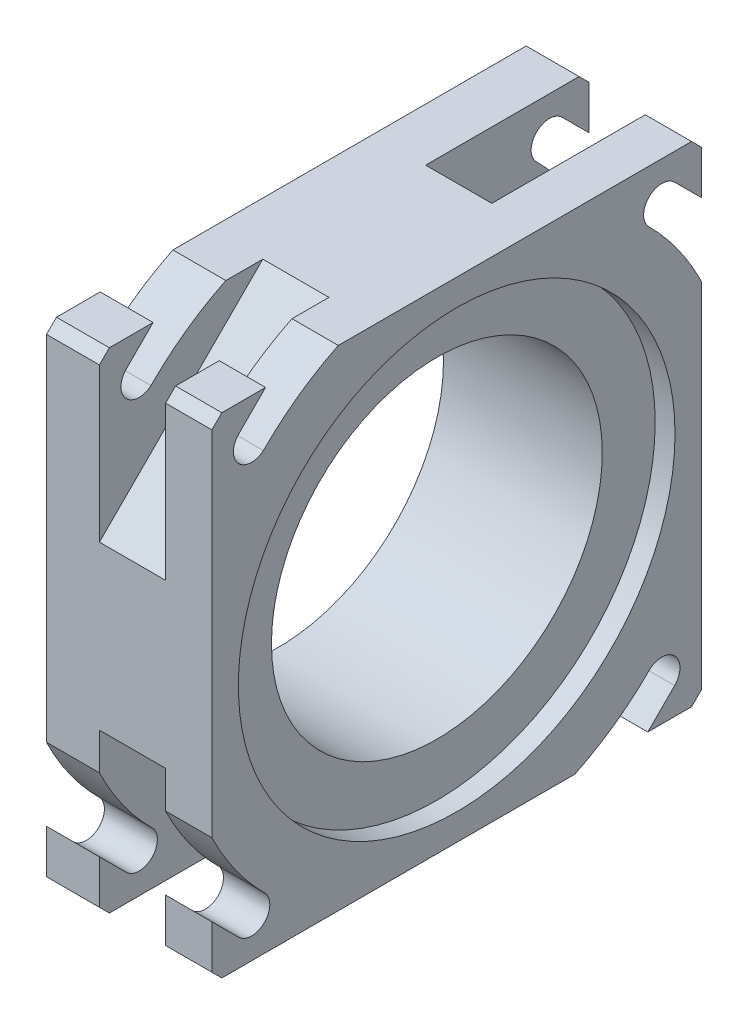
SolidWorks part; units mm, degrees
material "7075-T6, Chapa (SS)"
ref_plane "Plano frontal" through (0, 0, 0) normal (0, 0, 1) x (1, 0, 0)
ref_plane "Plano superior" through (0, 0, 0) normal (0, 1, 0) x (1, 0, 0)
ref_plane "Plano direito" through (0, 0, 0) normal (1, 0, 0) x (0, 0, -1)
sketch "Esboço1" plane through (0, 0, 0) normal (1, 0, 0) x (0, 0, -1)
  line L1 (0, 0) -> (74, 0)
  line L2 (0, 0) -> (0, 74)
  line L3 (0, 74) -> (74, 74)
  line L4 (74, 0) -> (74, 74)
  dimension "D1" = 74
  dimension "D2" = 74
extrude "Ressalto-extrusão1" add sketch "Esboço1" along normal blind 25
chamfer "Chanfro1" distance 1.5 angle 45 4 edges at (12.5, 0, 0) (12.5, 0, -74) (12.5, 74, 0) (12.5, 74, -74)
hole_wizard "Rebaixo para parafuso com cabeça panela de M21" positions "Esboço2" profile "Esboço3" counterbore size "M2" standard "ISO"
sketch "Esboço2" plane through (25, 0, 0) normal (1, 0, 0) x (0, 0, -1)
  point P0 (37, 37)
sketch "Esboço3" plane through (25, 37, -37) normal (0, 1, 0) x (0, 0, -1)
  line L0 (0, 0) -> (0, 50.0215)
  line L1 (0, 50.0215) -> (25, 35)
  line L2 (25, 35) -> (25, 3)
  line L3 (25, 3) -> (33, 3)
  line L4 (33, 3) -> (33, 0)
  line L5 (33, 0) -> (0, 0)
  line L10 (0, 50.0215) -> (-25, 35) construction
  line L11 (0, -6.35) -> (0, 107.95) construction
  dimension "Hole Dia." = 50
  dimension "Hole Depth" = 35
  dimension "C'Bore Dia." = 66
  dimension "C'Bore Depth" = 3
  dimension "Drill Angle" = 118
ref_plane "Plano1" through (0, 12.3466, -12.3466) normal (0, -0.7071, 0.7071) x (1, 0, 0)
sketch "Esboço4" plane through (0, 12.3466, -12.3466) normal (0, -0.7071, 0.7071) x (1, 0, 0)
  line L1 (8, 25) -> (18, 25)
  line L2 (8, 25) -> (8, -25)
  line L3 (8, -25) -> (18, -25)
  line L4 (18, 25) -> (18, -25)
  line L6 (25, -1.0607) -> (25, -51.2652) construction
  point P7 (18, 0)
  dimension "D1" = 10
  dimension "D2" = 7
  dimension "D3" = 50
extrude "Corte-extrusão1" cut sketch "Esboço4" along normal up to next (16.4 mm away)
sketch "Esboço5" plane through (25, 0, 0) normal (1, 0, 0) x (0, 0, -1)
  line L0 (37, 12) -> (37, 62) construction
  line L1 (12, 37) -> (62, 37) construction
  line L2 (19.3223, 54.6777) -> (54.6777, 19.3223) construction
  line L3 (37, 37) -> (54.6777, 54.6777) construction
  circle A0 centre (37, 37) radius 25 construction
  point P9 (37, 37)
  point P10 (37, 37)
  dimension "D1" = 45
  dimension "D2" = 45
ref_plane "Plano2" through (0, 37, -37) normal (0, -0.7071, 0.7071) x (0, -0.7071, -0.7071)
mirror "Espelhar1" about plane through (0, 37, -37) normal (0, -0.7071, 0.7071) of "Corte-extrusão1"
ref_plane "Plano3" through (0, 0, 0) normal (0, -0.7071, -0.7071) x (0, 0.7071, -0.7071)
ref_plane "Plano4" through (0, -24.6534, -24.6534) normal (0, -0.7071, -0.7071) x (-1, 0, 0)
sketch "Esboço6" plane through (0, -36.25, -36.25) normal (0, -0.7071, -0.7071) x (1, 0, 0)
  line L0 (25, -53.3866) -> (25, -103.5911) construction
  line L1 (8, -27.3259) -> (18, -27.3259)
  line L2 (8, -27.3259) -> (8, -77.3259)
  line L3 (8, -77.3259) -> (18, -77.3259)
  line L4 (18, -27.3259) -> (18, -77.3259)
  line L5 (0, -53.3866) -> (0, -51.2652) construction
  point P6 (0, -52.3259)
  point P7 (8, -52.3259)
  dimension "D1" = 7
  dimension "D2" = 10
  dimension "D3" = 50
extrude "Corte-extrusão2" cut sketch "Esboço6" along direction (0, -0.7071, -0.7071) on the side against the normal up to surface (16.4 mm away) contours L4 L3 L2 L1 up to plane "Plano4"
ref_plane "Plano5" through (0, 24.6534, 24.6534) normal (0, 0.7071, 0.7071) x (1, 0, 0)
sketch "Esboço11" plane through (0, 24.6534, 24.6534) normal (0, 0.7071, 0.7071) x (1, 0, 0)
  line L0 (25, 51.2652) -> (25, 1.0607) construction
  line L1 (8, 77.3259) -> (18, 77.3259)
  line L2 (8, 77.3259) -> (8, 27.3259)
  line L3 (8, 27.3259) -> (18, 27.3259)
  line L4 (18, 77.3259) -> (18, 27.3259)
  line L5 (25, 53.3866) -> (25, 51.2652) construction
  point P6 (18, 52.3259)
  point P9 (25, 52.3259)
  dimension "D1" = 7
  dimension "D2" = 10
  dimension "D3" = 50
extrude "Corte-extrusão4" cut sketch "Esboço11" along normal up to next
sketch "Esboço9" plane through (25, 0, 0) normal (1, 0, 0) x (0, 0, -1)
  line L0 (4.0555, 69.9445) -> (8.1109, 74)
  line L1 (72.5, 74) -> (1.5, 74) construction
  line L2 (7.4689, 65.6752) -> (7.6973, 65.8195)
  line L3 (0, 72.5) -> (0, 1.5) construction
  line L12 (1.5, 74) -> (0, 72.5) construction
  line L13 (8.1109, 74) -> (19.1056, 74)
  arc A0 (4.0555, 69.9445) -> (8.0937, 66.217) centre (6, 68) ccw
  circle A4 centre (37, 37) radius 41.1
  circle A5 centre (37, 37) radius 25 construction
  line M10 (72.5, 74) -> (1.5, 74)
  dimension "D2" = 5.5
  dimension "D4" = 82.2
  dimension "D3" = 6
extrude "Corte-extrusão3" cut sketch "Esboço9" against normal blind 7 contours A4 L0 A0 M10
pattern_circular "PadrãoCircular1" count 4 over 360 about axis through (0, 37, -37) along (1, 0, 0) of "Corte-extrusão3"
sketch "Esboço13" plane through (0, 0, 0) normal (-1, 0, 0) x (0, 0, 1)
  circle A0 centre (-37, 37) radius 33
  circle A1 centre (-37, 37) radius 25
  dimension "D1" = 66
  dimension "D2" = 50
extrude "Ressalto-extrusão2" add sketch "Esboço13" along normal blind 2
sketch "Esboço14" plane through (-2, 0, 0) normal (-1, 0, 0) x (0, 0, 1)
  circle A0 centre (-37, 37) radius 35.5
  circle A1 centre (-37, 37) radius 33
  dimension "D1" = 71
extrude "Corte-extrusão5" cut sketch "Esboço14" against normal blind 3.5 contours A0
sketch "Esboço16" plane through (0, 0, 0) normal (-1, 0, 0) x (0, 0, 1)
  line L0 (-4.0555, 69.9445) -> (-8.1109, 74)
  line L1 (-8.1109, 74) -> (-19.1056, 74)
  circle A0 centre (-37, 37) radius 41.1
  arc A1 (-8.0937, 66.217) -> (-4.0555, 69.9445) centre (-6, 68) ccw
extrude "Corte-extrusão10" cut sketch "Esboço16" against normal blind 8
pattern_circular "PadrãoCircular2" count 4 every 90 about axis through (0, 37, -37) along (1, 0, 0) of "Corte-extrusão10"
fillet "Filete1" radius 0.25 2 edges at (1.5, 37, -1.5) (1.5, 37, -4)
fillet "Filete2" radius 0.15 1 edges at (0, 37, -1.5)
